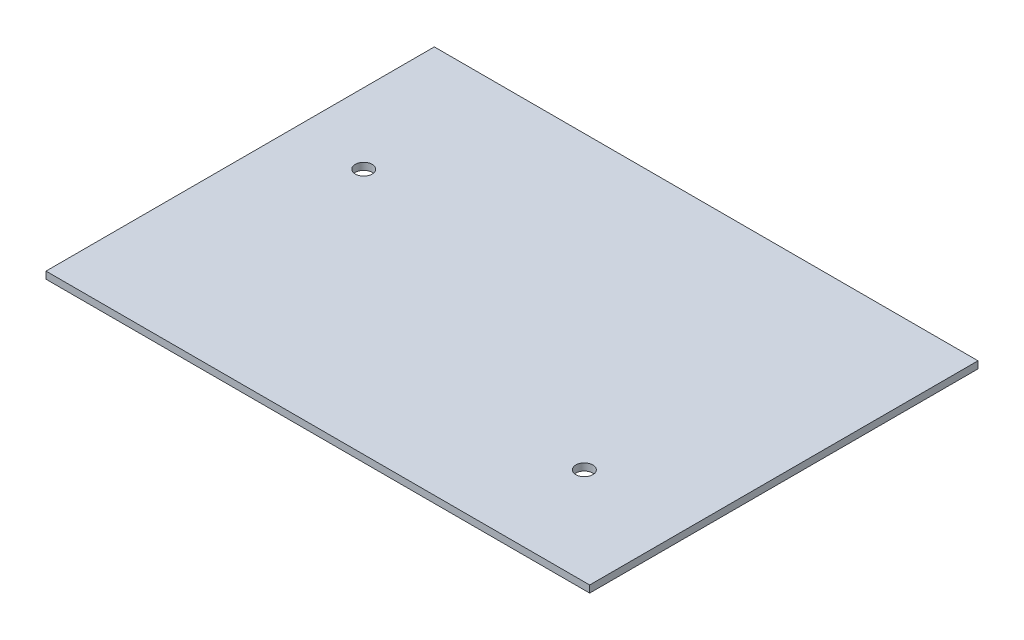
SolidWorks part; units mm, degrees
ref_plane "Front" through (0, 0, 0) normal (0, 0, 1) x (1, 0, 0)
ref_plane "Top" through (0, 0, 0) normal (0, 1, 0) x (1, 0, 0)
ref_plane "Right" through (0, 0, 0) normal (1, 0, 0) x (0, 0, -1)
sketch "Sketch1" plane through (0, 0, 0) normal (0, 1, 0) x (1, 0, 0)
  line L1 (-60.3092, 23.6513) -> (37.4808, 23.6513)
  line L2 (-60.3092, 23.6513) -> (-60.3092, -46.1987)
  line L3 (-60.3092, -46.1987) -> (37.4808, -46.1987)
  line L4 (37.4808, 23.6513) -> (37.4808, -46.1987)
  dimension "D1" = 97.79
  dimension "D2" = 69.85
extrude "Extrude1" add sketch "Sketch1" along normal blind 1.27
hole_wizard "Tap Drill for #4 Helicoil1" positions "3DSketch1" profile "Sketch2" hole size "#4-40" standard "Ansi Inch"
sketch3d "3DSketch1"
  line L0 (-60.3092, 1.27, -23.6513) -> (-60.3092, 1.27, 46.1987) construction
  line L1 (-60.3092, 1.27, 46.1987) -> (37.4808, 1.27, 46.1987) construction
  line L2 (37.4808, 1.27, 46.1987) -> (37.4808, 1.27, -23.6513) construction
  point P0 (19.0658, 1.27, 28.7362)
  point P2 (-47.6092, 1.27, 1.7487)
  dimension "D1" = 12.7
  dimension "D2" = 44.45
  dimension "D3" = 18.415
  dimension "D4" = 17.4625
sketch "Sketch2" plane through (19.0658, 1.27, 28.7362) normal (1, 0, 0) x (0, 0, 1)
  line L0 (0, 0) -> (0, 26.3157)
  line L1 (0, 26.3157) -> (1.524, 25.4)
  line L2 (1.524, 25.4) -> (1.524, 0)
  line L5 (1.524, 0) -> (0, 0)
  line L10 (0, 26.3157) -> (-1.524, 25.4) construction
  line L11 (0, -6.35) -> (0, 107.95) construction
  dimension "Hole Dia." = 3.048
  dimension "Hole Depth" = 25.4
  dimension "Drill Angle" = 118
